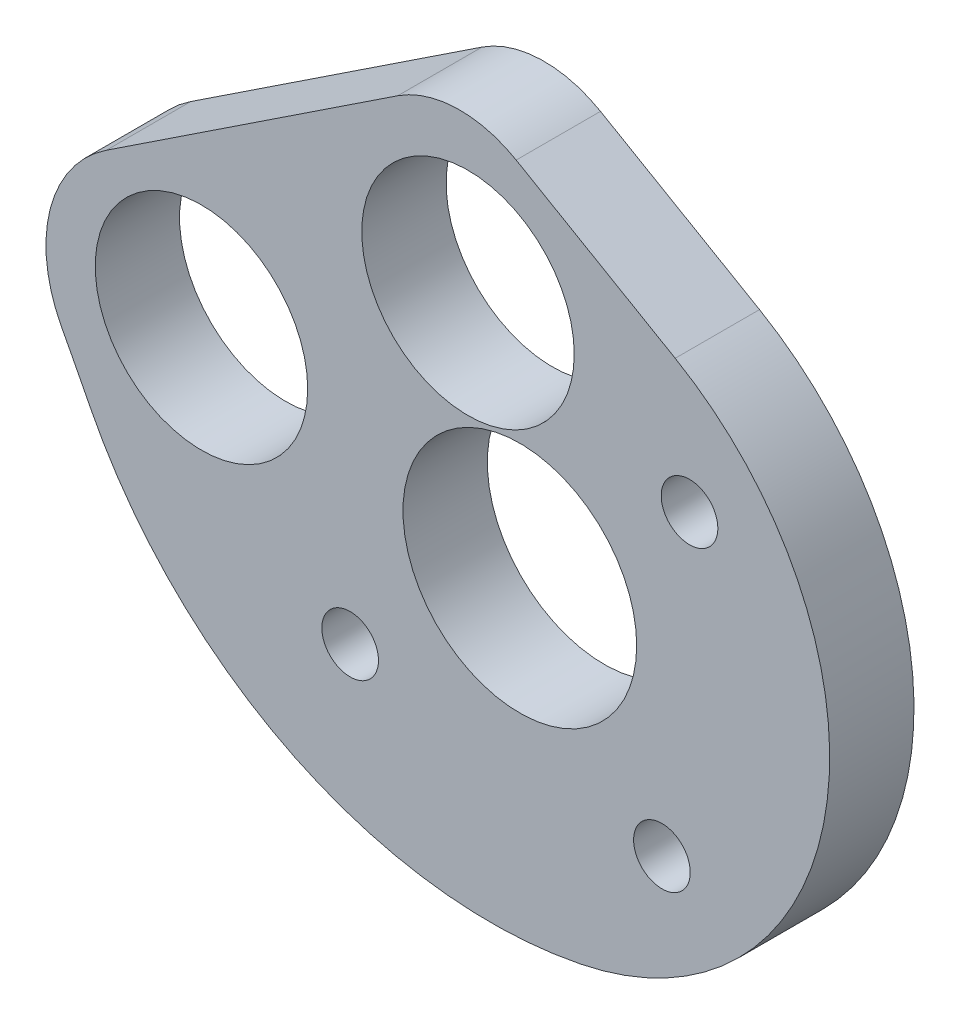
SolidWorks part; units mm, degrees
ref_plane "Front Plane" through (0, 0, 0) normal (0, 0, 1) x (1, 0, 0)
ref_plane "Top Plane" through (0, 0, 0) normal (0, 1, 0) x (1, 0, 0)
ref_plane "Right Plane" through (0, 0, 0) normal (1, 0, 0) x (0, 0, -1)
sketch "Sketch1" plane through (0, 0, 0) normal (0, 0, 1) x (1, 0, 0)
  line L0 (179.1481, 103.6071) -> (195.6033, 114.5003)
  line L2 (173.283, 99.7245) -> (184.5174, 97.6189) construction
  line L3 (202.4991, 94.3534) -> (199.5713, 106.8418) construction
  line L4 (199.5713, 106.8418) -> (184.5174, 97.6189) construction
  line L5 (202.4991, 94.3534) -> (212.083, 102.3782) construction
  line L6 (202.4991, 94.3534) -> (210.5239, 84.7694) construction
  line L7 (202.2925, 114.6994) -> (211.2738, 109.4945)
  line L8 (205.8738, 77.1817) -> (205.9408, 77.1951)
  circle A1 centre (184.5174, 97.6189) radius 6.0008
  circle A2 centre (199.5713, 106.8418) radius 6.0008
  circle A3 centre (202.4991, 94.3534) radius 12.5 construction
  circle A4 centre (212.083, 102.3782) radius 1.6
  circle A5 centre (210.5239, 84.7694) radius 1.6
  circle A6 centre (192.9151, 86.3286) radius 1.6
  arc A8 (176.6226, 93.6827) -> (178.2346, 90.5782) centre (0, 0) cw
  circle A9 centre (202.4991, 94.3534) radius 6.6
  arc A10 (205.9408, 77.1951) -> (211.2738, 109.4945) centre (202.4991, 94.3534) ccw
  arc A11 (202.2925, 114.6994) -> (195.6033, 114.5003) centre (199.1085, 109.2054) ccw
  arc A12 (179.1481, 103.6071) -> (176.6226, 93.6827) centre (183.3543, 97.2532) ccw
  arc A13 (205.8738, 77.1817) -> (178.2346, 90.5782) centre (200.8784, 102.0856) cw
  point P1 (198.8862, 116.6735)
  dimension "D10" = 12.0015
  dimension "D11" = 12.0015
  dimension "D12" = 25
  dimension "D13" = 3.2
  dimension "D16" = 13.2
  dimension "D17" = 35
  dimension "D2" = 6.35
  dimension "D3" = 7.62
  dimension "D18" = 25.4
  dimension "D4" = 44.12
  dimension "D5" = 137.89
  dimension "D6" = 17.6545
  dimension "D7" = 12.827
  dimension "D8" = 11.43
  dimension "D9" = 71.7
  dimension "D15" = 90
  dimension "D14" = 3
extrude "Boss-Extrude1" add sketch "Sketch1" along normal blind 4.7625
